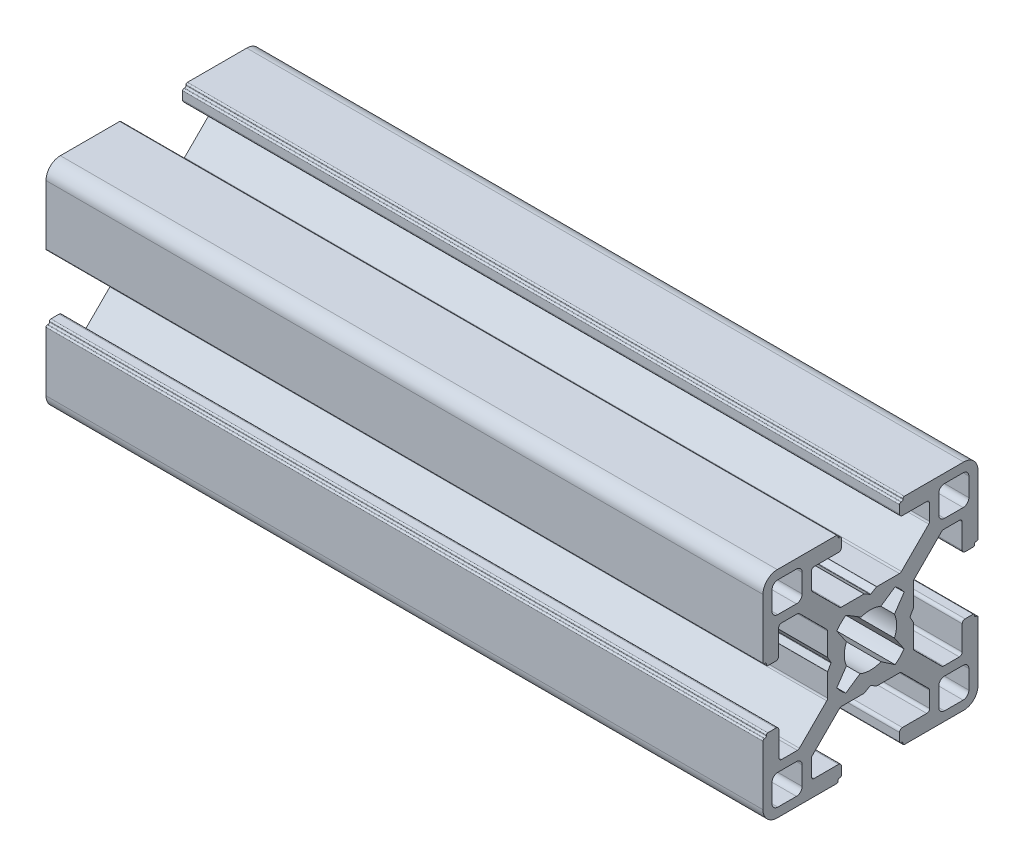
SolidWorks part; units mm, degrees
ref_plane "Front Plane" through (0, 0, 0) normal (0, 0, 1) x (1, 0, 0)
ref_plane "Top Plane" through (0, 0, 0) normal (0, 1, 0) x (1, 0, 0)
ref_plane "Right Plane" through (0, 0, 0) normal (1, 0, 0) x (0, 0, -1)
sketch "Sketch2" plane through (0, 0, 0) normal (1, 0, 0) x (0, 0, -1)
  line L0 (0.0324, 5.5172) -> (0.8252, 5.9749)
  line L1 (-13.0176, 14.9883) -> (-4.7476, 14.9883)
  line L2 (-15.0176, 12.9883) -> (-15.0176, 4.7183)
  line L3 (-13.0176, -15.0117) -> (-4.7476, -15.0117)
  line L4 (14.9824, 12.9883) -> (14.9824, 4.7183)
  line L5 (-15.0176, 14.9883) -> (-4.0847, 4.0554) construction
  line L6 (-15.0176, -15.0117) -> (-4.0861, -4.0802) construction
  line L7 (-0.0676, 5.5172) -> (-0.8604, 5.9749)
  line L8 (0.8752, 5.9883) -> (4.0207, 5.9883)
  line L9 (5.5113, 0.0383) -> (5.969, 0.8311)
  line L10 (5.5113, -0.0617) -> (5.969, -0.8545)
  line L11 (5.9824, -0.9045) -> (5.9824, -4.05)
  line L12 (0.8252, -5.9983) -> (0.0324, -5.5406)
  line L13 (-0.0676, -5.5406) -> (-0.8604, -5.9983)
  line L14 (-0.9104, -6.0117) -> (-4.0559, -6.0117)
  line L15 (-5.9866, -0.8428) -> (-5.5289, -0.05)
  line L16 (-4.0676, 14.3083) -> (-4.0676, 13.1883)
  line L21 (-6.0176, 5.9883) -> (-4.0847, 4.0554) construction
  line L22 (-6, -6) -> (-4.0832, -4.0832) construction
  line L23 (-4.4676, 12.7883) -> (-7.8676, 12.7883)
  line L24 (-8.2676, 12.3883) -> (-8.2676, 10.2)
  line L25 (-8.1505, 9.9172) -> (-4.3387, 6.1055)
  line L26 (-4.0559, 5.9883) -> (-0.9104, 5.9883)
  line L27 (4.3035, 6.1055) -> (8.1152, 9.9172)
  line L28 (8.2324, 10.2) -> (8.2324, 12.3883)
  line L29 (4.0324, 13.1883) -> (4.0324, 14.3083)
  line L30 (4.7124, 14.9883) -> (12.9824, 14.9883)
  line L31 (-5.5289, 0.05) -> (-5.9866, 0.8428)
  line L32 (4.4324, 12.7883) -> (7.8324, 12.7883)
  line L33 (14.3024, 4.0383) -> (13.1824, 4.0383)
  line L34 (12.7824, 4.4383) -> (12.7824, 7.8383)
  line L35 (12.3824, 8.2383) -> (10.1941, 8.2383)
  line L36 (9.9113, 8.1211) -> (6.0995, 4.3094)
  line L37 (5.9824, 4.0266) -> (5.9824, 0.8811)
  line L38 (6.0995, -4.3328) -> (9.9113, -8.1445)
  line L39 (10.1941, -8.2617) -> (12.3824, -8.2617)
  line L40 (12.7824, -7.8617) -> (12.7824, -4.4617)
  line L41 (13.1824, -4.0617) -> (14.3024, -4.0617)
  line L42 (14.9824, -4.7417) -> (14.9824, -13.0117)
  line L43 (-6, 0.8928) -> (-6, 4.0383)
  line L44 (4.0324, -14.3317) -> (4.0324, -13.2117)
  line L45 (4.4324, -12.8117) -> (7.8324, -12.8117)
  line L46 (8.2324, -12.4117) -> (8.2324, -10.2234)
  line L47 (8.1152, -9.9406) -> (4.3035, -6.1289)
  line L48 (4.0207, -6.0117) -> (0.8752, -6.0117)
  line L49 (-4.3387, -6.1289) -> (-8.1505, -9.9406)
  line L50 (-8.2676, -10.2234) -> (-8.2676, -12.4117)
  line L51 (-7.8676, -12.8117) -> (-4.4676, -12.8117)
  line L52 (-4.0676, -13.2117) -> (-4.0676, -14.3317)
  line L53 (4.7124, -15.0117) -> (12.9824, -15.0117)
  line L54 (-14.3376, -4.0617) -> (-13.2, -4.0617)
  line L55 (-12.8, -4.4617) -> (-12.8, -7.85)
  line L56 (-12.4, -8.25) -> (-10.2117, -8.25)
  line L57 (-9.9289, -8.1328) -> (-6.1172, -4.3211)
  line L58 (-6, -4.0383) -> (-6, -0.8928)
  line L59 (-6.1172, 4.3211) -> (-9.9289, 8.1328)
  line L60 (-10.2117, 8.25) -> (-12.4176, 8.25)
  line L61 (-12.8176, 7.85) -> (-12.8176, 4.4383)
  line L62 (-13.2176, 4.0383) -> (-14.3376, 4.0383)
  line L63 (-15.0176, -4.7417) -> (-15.0176, -13.0117)
  line L66 (10.3103, 9.5162) -> (12.9103, 9.5162)
  line L67 (9.5103, 10.3162) -> (9.5103, 12.9162)
  line L69 (-12.9456, -13.7397) -> (-10.3456, -13.7397)
  line L70 (-12.9456, 13.7162) -> (-10.3456, 13.7162)
  line L71 (-13.7456, 12.9162) -> (-13.7456, 10.3162)
  line L72 (-12.9456, 9.5162) -> (-10.3456, 9.5162)
  line L73 (-9.5456, 12.9162) -> (-9.5456, 10.3162)
  line L74 (-13.7456, 13.7162) -> (-9.5456, 9.5162) construction
  line L75 (-13.7456, 9.5162) -> (-9.5456, 13.7162) construction
  line L76 (-13.7456, -12.9397) -> (-13.7456, -10.3397)
  line L77 (-12.9456, -9.5397) -> (-10.3456, -9.5397)
  line L78 (-9.5456, -12.9397) -> (-9.5456, -10.3397)
  line L79 (-13.7456, -13.7397) -> (-9.5456, -9.5397) construction
  line L80 (-13.7456, -9.5397) -> (-9.5456, -13.7397) construction
  line L81 (10.3103, -9.5397) -> (12.9103, -9.5397)
  line L82 (9.5103, -10.3397) -> (9.5103, -12.9397)
  line L83 (10.3103, -13.7397) -> (12.9103, -13.7397)
  line L84 (13.7103, -10.3397) -> (13.7103, -12.9397)
  line L85 (9.5103, -9.5397) -> (13.7103, -13.7397) construction
  line L86 (9.5103, -13.7397) -> (13.7103, -9.5397) construction
  line L87 (10.3103, 13.7162) -> (12.9103, 13.7162)
  line L88 (13.7103, 10.3162) -> (13.7103, 12.9162)
  line L89 (9.5103, 9.5162) -> (13.7103, 13.7162) construction
  line L90 (9.5103, 13.7162) -> (13.7103, 9.5162) construction
  line L93 (-3.4484, 4.6917) -> (-1.3098, 3.4019)
  line L94 (-4.721, 3.4191) -> (-3.3678, 1.4369)
  line L95 (-4.719, -3.4473) -> (-3.3678, -1.4604)
  line L96 (-3.4533, -4.7131) -> (-1.4712, -3.3598)
  line L97 (3.4156, -4.7115) -> (1.436, -3.3598)
  line L98 (4.6822, -3.4449) -> (3.3326, -1.4604)
  line L99 (4.6838, 3.4239) -> (3.3326, 1.4369)
  line L100 (3.418, 4.6897) -> (1.436, 3.3364)
  line L103 (4.0509, 4.0568) -> (14.9824, 14.9883) construction
  line L104 (4.0539, 4.0539) -> (6, 6) construction
  line L105 (2.5633, -2.5926) -> (5.9824, -6.0117) construction
  line L106 (2.5633, -2.5926) -> (14.9824, -15.0117) construction
  line L109 (-4.5476, 14.7883) -> (-4.5476, 14.7083)
  line L110 (-4.3476, 14.5083) -> (-4.2676, 14.5083)
  line L111 (4.5124, 14.7883) -> (4.5124, 14.7083)
  line L112 (4.3124, 14.5083) -> (4.2324, 14.5083)
  line L113 (14.7824, 4.5183) -> (14.7024, 4.5183)
  line L114 (14.5024, 4.3183) -> (14.5024, 4.2383)
  line L115 (14.7824, -4.5417) -> (14.7024, -4.5417)
  line L116 (14.5024, -4.3417) -> (14.5024, -4.2617)
  line L117 (4.2324, -14.5317) -> (4.3124, -14.5317)
  line L118 (4.5124, -14.7317) -> (4.5124, -14.8117)
  line L119 (-4.5476, -14.8117) -> (-4.5476, -14.7317)
  line L120 (-4.3476, -14.5317) -> (-4.2676, -14.5317)
  line L121 (-14.8176, -4.5417) -> (-14.7376, -4.5417)
  line L122 (-14.5376, -4.3417) -> (-14.5376, -4.2617)
  line L123 (-14.5376, 4.2383) -> (-14.5376, 4.3183)
  line L124 (-14.7376, 4.5183) -> (-14.8176, 4.5183)
  arc A0 (-13.0176, 14.9883) -> (-15.0176, 12.9883) centre (-13.0176, 12.9883) ccw
  arc A1 (-15.0176, -13.0117) -> (-13.0176, -15.0117) centre (-13.0176, -13.0117) ccw
  arc A2 (12.9824, -15.0117) -> (14.9824, -13.0117) centre (12.9824, -13.0117) ccw
  arc A3 (12.9824, 14.9883) -> (14.9824, 12.9883) centre (12.9824, 12.9883) cw
  arc A4 (-13.7456, 10.3162) -> (-12.9456, 9.5162) centre (-12.9456, 10.3162) ccw
  arc A5 (-10.3456, 9.5162) -> (-9.5456, 10.3162) centre (-10.3456, 10.3162) ccw
  arc A6 (-10.3456, 13.7162) -> (-9.5456, 12.9162) centre (-10.3456, 12.9162) cw
  arc A7 (-12.9456, 13.7162) -> (-13.7456, 12.9162) centre (-12.9456, 12.9162) ccw
  arc A8 (12.9103, 9.5162) -> (13.7103, 10.3162) centre (12.9103, 10.3162) ccw
  arc A9 (10.3103, 9.5162) -> (9.5103, 10.3162) centre (10.3103, 10.3162) cw
  arc A10 (12.9103, 13.7162) -> (13.7103, 12.9162) centre (12.9103, 12.9162) cw
  arc A11 (9.5103, 12.9162) -> (10.3103, 13.7162) centre (10.3103, 12.9162) cw
  arc A12 (9.5103, -12.9397) -> (10.3103, -13.7397) centre (10.3103, -12.9397) ccw
  arc A13 (12.9103, -13.7397) -> (13.7103, -12.9397) centre (12.9103, -12.9397) ccw
  arc A14 (12.9103, -9.5397) -> (13.7103, -10.3397) centre (12.9103, -10.3397) cw
  arc A15 (10.3103, -9.5397) -> (9.5103, -10.3397) centre (10.3103, -10.3397) ccw
  arc A16 (-12.9456, -13.7397) -> (-13.7456, -12.9397) centre (-12.9456, -12.9397) cw
  arc A17 (-10.3456, -13.7397) -> (-9.5456, -12.9397) centre (-10.3456, -12.9397) ccw
  arc A18 (-10.3456, -9.5397) -> (-9.5456, -10.3397) centre (-10.3456, -10.3397) cw
  arc A19 (-13.7456, -10.3397) -> (-12.9456, -9.5397) centre (-12.9456, -10.3397) cw
  arc A20 (-3.3678, 1.4369) -> (-3.3678, -1.4604) centre (-0.0176, -0.0117) ccw
  arc A21 (1.436, 3.3364) -> (-1.3098, 3.4019) centre (-0.0176, -0.0117) ccw
  arc A22 (2.5663, 2.5663) -> (2.5633, 2.5692) centre (-0.0176, -0.0117) ccw
  arc A23 (3.3326, -1.4604) -> (3.3326, 1.4369) centre (-0.0176, -0.0117) ccw
  arc A24 (-1.4712, -3.3598) -> (1.436, -3.3598) centre (-0.0176, -0.0117) ccw
  arc A25 (-2.5985, -2.5926) -> (-2.5956, -2.5956) centre (-0.0176, -0.0117) ccw
  arc A26 (-4.5476, 14.7083) -> (-4.3476, 14.5083) centre (-4.3476, 14.7083) ccw
  arc A27 (-4.2676, 14.5083) -> (-4.0676, 14.3083) centre (-4.2676, 14.3083) cw
  arc A28 (-4.5476, 14.7883) -> (-4.7476, 14.9883) centre (-4.7476, 14.7883) ccw
  arc A29 (4.5124, 14.7883) -> (4.7124, 14.9883) centre (4.7124, 14.7883) cw
  arc A30 (4.5124, 14.7083) -> (4.3124, 14.5083) centre (4.3124, 14.7083) cw
  arc A31 (4.2324, 14.5083) -> (4.0324, 14.3083) centre (4.2324, 14.3083) ccw
  arc A32 (14.7824, 4.5183) -> (14.9824, 4.7183) centre (14.7824, 4.7183) ccw
  arc A33 (14.7024, 4.5183) -> (14.5024, 4.3183) centre (14.7024, 4.3183) ccw
  arc A34 (14.5024, 4.2383) -> (14.3024, 4.0383) centre (14.3024, 4.2383) cw
  arc A35 (14.5024, -4.2617) -> (14.3024, -4.0617) centre (14.3024, -4.2617) ccw
  arc A36 (14.7024, -4.5417) -> (14.5024, -4.3417) centre (14.7024, -4.3417) cw
  arc A37 (14.7824, -4.5417) -> (14.9824, -4.7417) centre (14.7824, -4.7417) cw
  arc A38 (4.2324, -14.5317) -> (4.0324, -14.3317) centre (4.2324, -14.3317) cw
  arc A39 (4.3124, -14.5317) -> (4.5124, -14.7317) centre (4.3124, -14.7317) cw
  arc A40 (4.5124, -14.8117) -> (4.7124, -15.0117) centre (4.7124, -14.8117) ccw
  arc A41 (-4.2676, -14.5317) -> (-4.0676, -14.3317) centre (-4.2676, -14.3317) ccw
  arc A42 (-4.5476, -14.7317) -> (-4.3476, -14.5317) centre (-4.3476, -14.7317) cw
  arc A43 (-4.5476, -14.8117) -> (-4.7476, -15.0117) centre (-4.7476, -14.8117) cw
  arc A44 (-14.5376, -4.2617) -> (-14.3376, -4.0617) centre (-14.3376, -4.2617) cw
  arc A45 (-14.7376, -4.5417) -> (-14.5376, -4.3417) centre (-14.7376, -4.3417) ccw
  arc A46 (-14.8176, -4.5417) -> (-15.0176, -4.7417) centre (-14.8176, -4.7417) ccw
  arc A47 (-14.8176, 4.5183) -> (-15.0176, 4.7183) centre (-14.8176, 4.7183) cw
  arc A48 (-14.5376, 4.3183) -> (-14.7376, 4.5183) centre (-14.7376, 4.3183) ccw
  arc A49 (-14.5376, 4.2383) -> (-14.3376, 4.0383) centre (-14.3376, 4.2383) ccw
  arc A50 (-7.8676, 12.7883) -> (-8.2676, 12.3883) centre (-7.8676, 12.3883) ccw
  arc A51 (-4.0676, 13.1883) -> (-4.4676, 12.7883) centre (-4.4676, 13.1883) cw
  arc A52 (13.1824, 4.0383) -> (12.7824, 4.4383) centre (13.1824, 4.4383) cw
  arc A53 (8.2324, 12.3883) -> (7.8324, 12.7883) centre (7.8324, 12.3883) ccw
  arc A54 (4.0324, 13.1883) -> (4.4324, 12.7883) centre (4.4324, 13.1883) ccw
  arc A55 (12.7824, 7.8383) -> (12.3824, 8.2383) centre (12.3824, 7.8383) ccw
  arc A56 (12.3824, -8.2617) -> (12.7824, -7.8617) centre (12.3824, -7.8617) ccw
  arc A57 (12.7824, -4.4617) -> (13.1824, -4.0617) centre (13.1824, -4.4617) cw
  arc A58 (7.8324, -12.8117) -> (8.2324, -12.4117) centre (7.8324, -12.4117) ccw
  arc A59 (4.0324, -13.2117) -> (4.4324, -12.8117) centre (4.4324, -13.2117) cw
  arc A60 (-4.4676, -12.8117) -> (-4.0676, -13.2117) centre (-4.4676, -13.2117) cw
  arc A61 (-8.2676, -12.4117) -> (-7.8676, -12.8117) centre (-7.8676, -12.4117) ccw
  arc A62 (-12.8, -7.85) -> (-12.4, -8.25) centre (-12.4, -7.85) ccw
  arc A63 (-13.2, -4.0617) -> (-12.8, -4.4617) centre (-13.2, -4.4617) cw
  arc A64 (-12.8176, 4.4383) -> (-13.2176, 4.0383) centre (-13.2176, 4.4383) cw
  arc A65 (-12.4176, 8.25) -> (-12.8176, 7.85) centre (-12.4176, 7.85) ccw
  arc A66 (-9.9289, 8.1328) -> (-10.2117, 8.25) centre (-10.2117, 7.85) ccw
  arc A67 (-8.2676, 10.2) -> (-8.1505, 9.9172) centre (-7.8676, 10.2) ccw
  arc A68 (8.1152, 9.9172) -> (8.2324, 10.2) centre (7.8324, 10.2) ccw
  arc A69 (10.1941, 8.2383) -> (9.9113, 8.1211) centre (10.1941, 7.8383) ccw
  arc A70 (8.2324, -10.2234) -> (8.1152, -9.9406) centre (7.8324, -10.2234) ccw
  arc A71 (9.9113, -8.1445) -> (10.1941, -8.2617) centre (10.1941, -7.8617) ccw
  arc A72 (-10.2117, -8.25) -> (-9.9289, -8.1328) centre (-10.2117, -7.85) ccw
  arc A73 (-8.1505, -9.9406) -> (-8.2676, -10.2234) centre (-7.8676, -10.2234) ccw
  arc A74 (6.0995, 4.3094) -> (5.9824, 4.0266) centre (6.3824, 4.0266) ccw
  arc A75 (4.0207, 5.9883) -> (4.3035, 6.1055) centre (4.0207, 6.3883) ccw
  arc A76 (-4.3387, 6.1055) -> (-4.0559, 5.9883) centre (-4.0559, 6.3883) ccw
  arc A77 (-6, 4.0383) -> (-6.1172, 4.3211) centre (-6.4, 4.0383) ccw
  arc A78 (-6.1172, -4.3211) -> (-6, -4.0383) centre (-6.4, -4.0383) ccw
  arc A79 (-4.0559, -6.0117) -> (-4.3387, -6.1289) centre (-4.0559, -6.4117) ccw
  arc A80 (4.3035, -6.1289) -> (4.0207, -6.0117) centre (4.0207, -6.4117) ccw
  arc A81 (5.9824, -4.05) -> (6.0995, -4.3328) centre (6.3824, -4.05) ccw
  arc A82 (-0.8604, 5.9749) -> (-0.9104, 5.9883) centre (-0.9104, 5.8883) ccw
  arc A83 (0.0324, 5.5172) -> (-0.0676, 5.5172) centre (-0.0176, 5.6038) cw
  arc A84 (0.8252, 5.9749) -> (0.8752, 5.9883) centre (0.8752, 5.8883) cw
  arc A85 (5.969, 0.8311) -> (5.9824, 0.8811) centre (5.8824, 0.8811) ccw
  arc A86 (5.5113, 0.0383) -> (5.5113, -0.0617) centre (5.5979, -0.0117) ccw
  arc A87 (5.969, -0.8545) -> (5.9824, -0.9045) centre (5.8824, -0.9045) cw
  arc A88 (0.8252, -5.9983) -> (0.8752, -6.0117) centre (0.8752, -5.9117) ccw
  arc A89 (0.0324, -5.5406) -> (-0.0676, -5.5406) centre (-0.0176, -5.6272) ccw
  arc A90 (-0.8604, -5.9983) -> (-0.9104, -6.0117) centre (-0.9104, -5.9117) cw
  arc A91 (-5.9866, -0.8428) -> (-6, -0.8928) centre (-5.9, -0.8928) ccw
  arc A92 (-5.5289, -0.05) -> (-5.5289, 0.05) centre (-5.6155, 0) ccw
  arc A93 (-5.9866, 0.8428) -> (-6, 0.8928) centre (-5.9, 0.8928) cw
  arc A94 (-4.721, 3.4191) -> (-3.4484, 4.6917) centre (-0.0176, -0.0117) cw
  arc A95 (4.6838, 3.4239) -> (3.418, 4.6897) centre (-0.0176, -0.0117) ccw
  arc A96 (3.4156, -4.7115) -> (4.6822, -3.4449) centre (-0.0176, -0.0117) ccw
  arc A97 (-4.719, -3.4473) -> (-3.4533, -4.7131) centre (-0.0176, -0.0117) ccw
  point P0 (0, 0)
  point P7 (11.6103, 11.6162)
  point P13 (11.6103, 11.6162)
  point P22 (-11.6456, -11.6397)
  point P23 (11.6103, -11.6397)
  point P29 (-11.6456, 11.6162)
  point P33 (0, 0)
  point P36 (0, 0)
  point P51 (0, 0)
  point P103 (0, 5.5)
  point P157 (-4.0847, 4.0554)
  point P160 (4.0509, 4.0568)
  point P163 (4.0489, -4.0782)
  point P166 (-4.0861, -4.0802)
  dimension "D19" = 0.2
  dimension "D1" = 2
  dimension "D2" = 2
  dimension "D7" = 0.8
  dimension "D8" = 0.8
  dimension "D9" = 0.8
  dimension "D10" = 0.8
  dimension "D11" = 7.3
  dimension "D12" = 0.2
  dimension "D13" = 0.2
  dimension "D14" = 0.2
  dimension "D15" = 0.2
  dimension "D16" = 0.2
  dimension "D17" = 0.2
  dimension "D18" = 0.2
  dimension "D20" = 0.4
  dimension "D21" = 0.4
  dimension "D22" = 0.4
  dimension "D23" = 0.4
  dimension "D24" = 0.4
  dimension "D25" = 0.4
  dimension "D26" = 0.4
  dimension "D27" = 0.4
  dimension "D28" = 0.4
  dimension "D29" = 0.4
  dimension "D30" = 0.4
  dimension "D31" = 0.4
  dimension "D32" = 0.4
  dimension "D33" = 0.4
  dimension "D34" = 0.4
  dimension "D35" = 0.1
  dimension "D3" = 4.2
  dimension "D4" = 4.2
  dimension "D5" = 4.2
  dimension "D6" = 4.2
extrude "Boss-Extrude2" add sketch "Sketch2" along normal blind 100 contours A93 L31 A92 L15 A91 L58 A78 L57 A72 L56 A62 L55 A63 L54 A44 L122 A45 L121 A46 L63 A1 L3 A43 L119 A42 L120 A41 L52 A60 L51 A61 L50 A73 L49 A79 L14 A90 L13 A89 L12 A88 L48 A80 L47 A70 L46 A58 L45 A59 L44 A38
